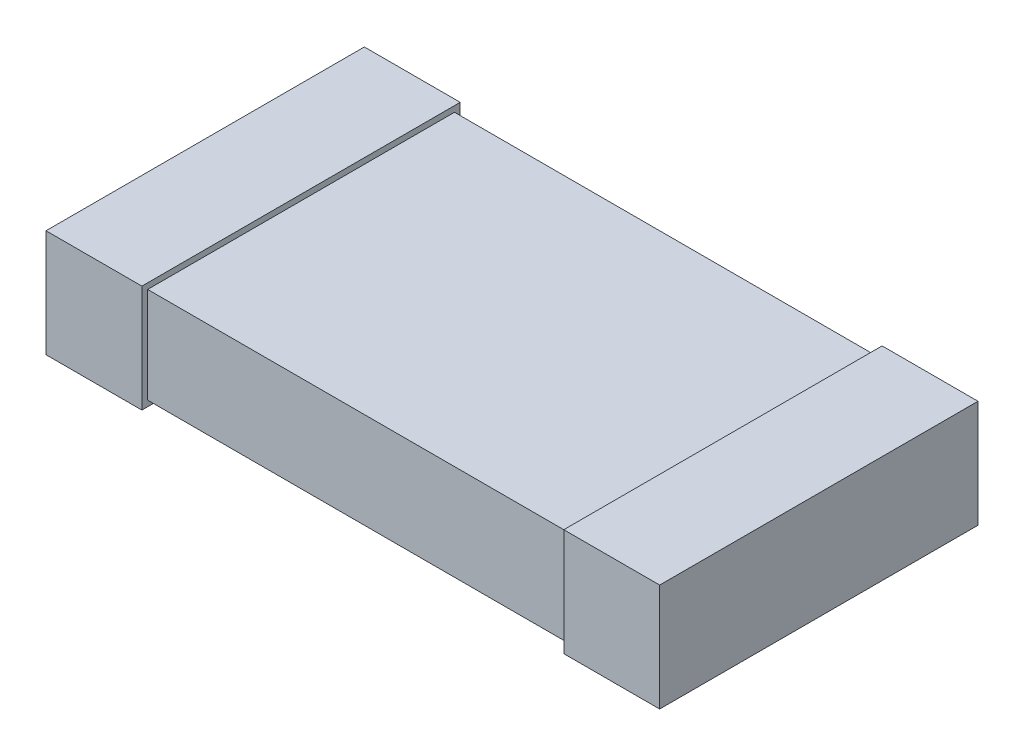
SolidWorks part; units mm, degrees
ref_plane "Front Plane" through (0, 0, 0) normal (0, 0, 1) x (1, 0, 0)
ref_plane "Top Plane" through (0, 0, 0) normal (0, 1, 0) x (1, 0, 0)
ref_plane "Right Plane" through (0, 0, 0) normal (1, 0, 0) x (0, 0, -1)
sketch "Sketch1" plane through (0, 0, 0) normal (0, 1, 0) x (1, 0, 0)
  line L1 (-1.6, 0.8) -> (1.6, 0.8)
  line L2 (-1.6, 0.8) -> (-1.6, -0.8)
  line L3 (-1.6, -0.8) -> (1.6, -0.8)
  line L4 (1.6, 0.8) -> (1.6, -0.8)
  point P4 (0, 0.8)
  point P6 (1.6, 0)
  dimension "D1" = 1.6
  dimension "D2" = 3.2
extrude "Extrude1" add sketch "Sketch1" along normal blind 0.5
sketch "Sketch2" plane through (0, 0, 0) normal (0, 0, 1) x (1, 0, 0)
  line L0 (-1.6, 0.5) -> (-1.6, 0) construction
  line L1 (-1.1, 0.53) -> (-1.6, 0.53)
  line L2 (-1.1, 0.53) -> (-1.1, -0.03)
  line L3 (-1.1, -0.03) -> (-1.6, -0.03)
  line L4 (-1.6, 0.53) -> (-1.6, -0.03)
  line L5 (-1.6, 0.5) -> (1.6, 0.5) construction
  line L6 (-1.6, 0) -> (1.6, 0) construction
  line L7 (0, 0) -> (0, -0.3575) construction
  line L8 (1.6, 0.53) -> (1.6, -0.03)
  line L9 (1.1, -0.03) -> (1.6, -0.03)
  line L10 (1.1, 0.53) -> (1.1, -0.03)
  line L11 (1.1, 0.53) -> (1.6, 0.53)
  dimension "D1" = 0.5
  dimension "D2" = 0.03
  dimension "D3" = 0.03
extrude "Extrude2" add sketch "Sketch2" along normal offset from surface 0.03 and the other way offset from surface (0.83 mm away) 0.03 up to face at (0, 0.25, 0.8) offset beyond the face yes other way up to face at (0, 0.25, -0.8)
ref_plane "Plane1" through (0, -0.03, 0) normal (0, 1, 0) x (-1, 0, 0)
sketch "Component_Outline" plane through (0, -0.03, 0) normal (0, 1, 0) x (-1, 0, 0)
  line L0 (1.6, 0.83) -> (1.1, 0.83)
  line L1 (1.1, 0.83) -> (1.1, 0.8)
  line L2 (1.1, 0.8) -> (-1.1, 0.8)
  line L3 (-1.1, 0.8) -> (-1.1, 0.83)
  line L4 (-1.1, 0.83) -> (-1.6, 0.83)
  line L5 (-1.6, 0.83) -> (-1.6, -0.83)
  line L6 (-1.6, -0.83) -> (-1.1, -0.83)
  line L7 (-1.1, -0.83) -> (-1.1, -0.8)
  line L8 (-1.1, -0.8) -> (1.1, -0.8)
  line L9 (1.1, 0.83) -> (1.1, -0.83) construction
  line L10 (1.1, -0.8) -> (1.1, 0.8) construction
  line L11 (1.1, -0.8) -> (1.1, -0.83)
  line L12 (1.1, -0.83) -> (1.6, -0.83)
  line L13 (1.6, -0.83) -> (1.6, 0.83)
